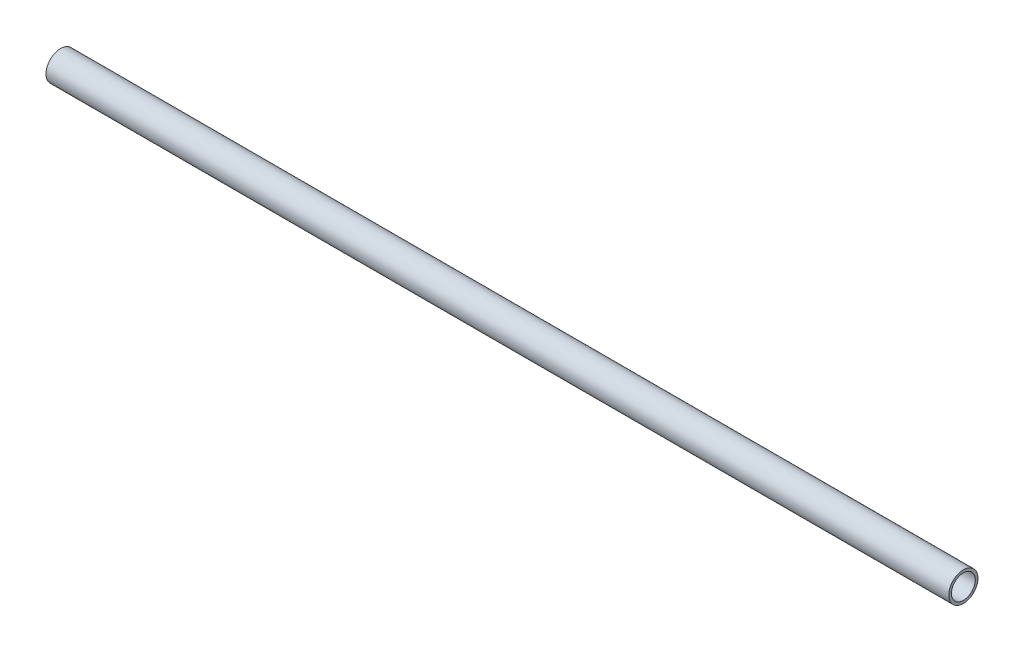
SolidWorks part; units mm, degrees
ref_plane "Front" through (0, 0, 0) normal (0, 0, 1) x (1, 0, 0)
ref_plane "Top" through (0, 0, 0) normal (0, 1, 0) x (1, 0, 0)
ref_plane "Right" through (0, 0, 0) normal (1, 0, 0) x (0, 0, -1)
sketch "Sketch1" plane through (0, 0, 0) normal (0, 1, 0) x (1, 0, 0)
  line L0 (-489.896, 0) -> (0, 0)
  dimension "D1" = 489.896
other "Structural Member1"
ref_plane "Plane1" through (-489.896, 0, 0) normal (1, 0, 0) x (0, 0, -1)
sketch "Sketch11" plane through (-489.896, 0, 0) normal (1, 0, 0) x (0, 0, -1)
  circle A0 centre (0, 0) radius 6.4643
  circle A1 centre (0, 0) radius 7.9375
  point P5 (0, 0)
  dimension "D1" = 1.4732
  dimension "D2" = 15.875
